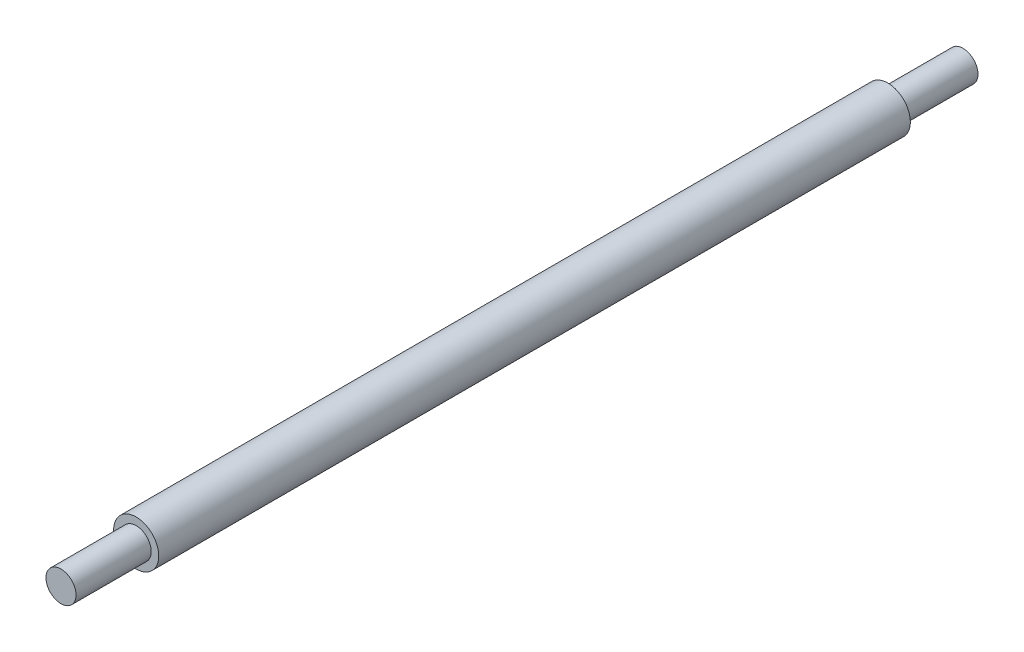
SolidWorks part; units mm, degrees
material "Plain Carbon Steel"
ref_plane "Front Plane" through (0, 0, 0) normal (0, 0, 1) x (1, 0, 0)
ref_plane "Top Plane" through (0, 0, 0) normal (0, 1, 0) x (1, 0, 0)
ref_plane "Right Plane" through (0, 0, 0) normal (1, 0, 0) x (0, 0, -1)
sketch "Sketch1" plane through (0, 0, 0) normal (0, 0, 1) x (1, 0, 0)
  circle A0 centre (0, 0) radius 19.05
  dimension "D1" = 38.1
extrude "Boss-Extrude1" add sketch "Sketch1" along normal blind 635
sketch "Sketch2" plane through (0, 0, 635) normal (0, 0, 1) x (1, 0, 0)
  circle A0 centre (0, 0) radius 12.7
  dimension "D1" = 25.4
extrude "Boss-Extrude2" add sketch "Sketch2" along normal blind 63.5
sketch "Sketch3" plane through (0, 0, 0) normal (0, 0, -1) x (-1, 0, 0)
  circle A0 centre (0, 0) radius 12.7
  dimension "D1" = 25.4
extrude "Boss-Extrude3" add sketch "Sketch3" along normal blind 63.5
